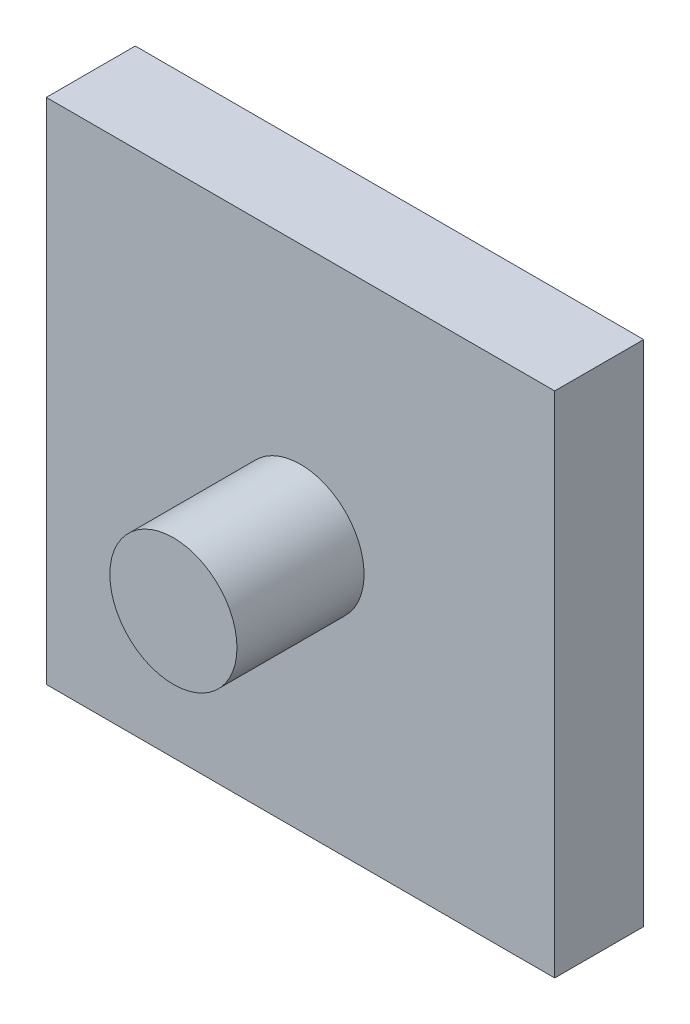
SolidWorks part; units mm, degrees
ref_plane "Plan de face" through (0, 0, 0) normal (0, 0, 1) x (1, 0, 0)
ref_plane "Plan de dessus" through (0, 0, 0) normal (0, 1, 0) x (1, 0, 0)
ref_plane "Plan de droite" through (0, 0, 0) normal (1, 0, 0) x (0, 0, -1)
sketch "Esquisse1" plane through (0, 0, 0) normal (0, 0, 1) x (1, 0, 0)
  line L0 (0, 0) -> (12.2962, 0) construction
  line L1 (-20, -20) -> (20, -20)
  line L2 (-20, -20) -> (-20, 20)
  line L3 (-20, 20) -> (20, 20)
  line L4 (20, -20) -> (20, 20)
  line L5 (0, 0) -> (0, 11.0899) construction
  dimension "D1" = 40
extrude "Boss.-Extru.1" add sketch "Esquisse1" along normal blind 7
sketch "Esquisse2" plane through (0, 0, 7) normal (0, 0, 1) x (1, 0, 0)
  circle A0 centre (0, 0) radius 5
  dimension "D1" = 10
extrude "Boss.-Extru.2" add sketch "Esquisse2" along normal blind 10
